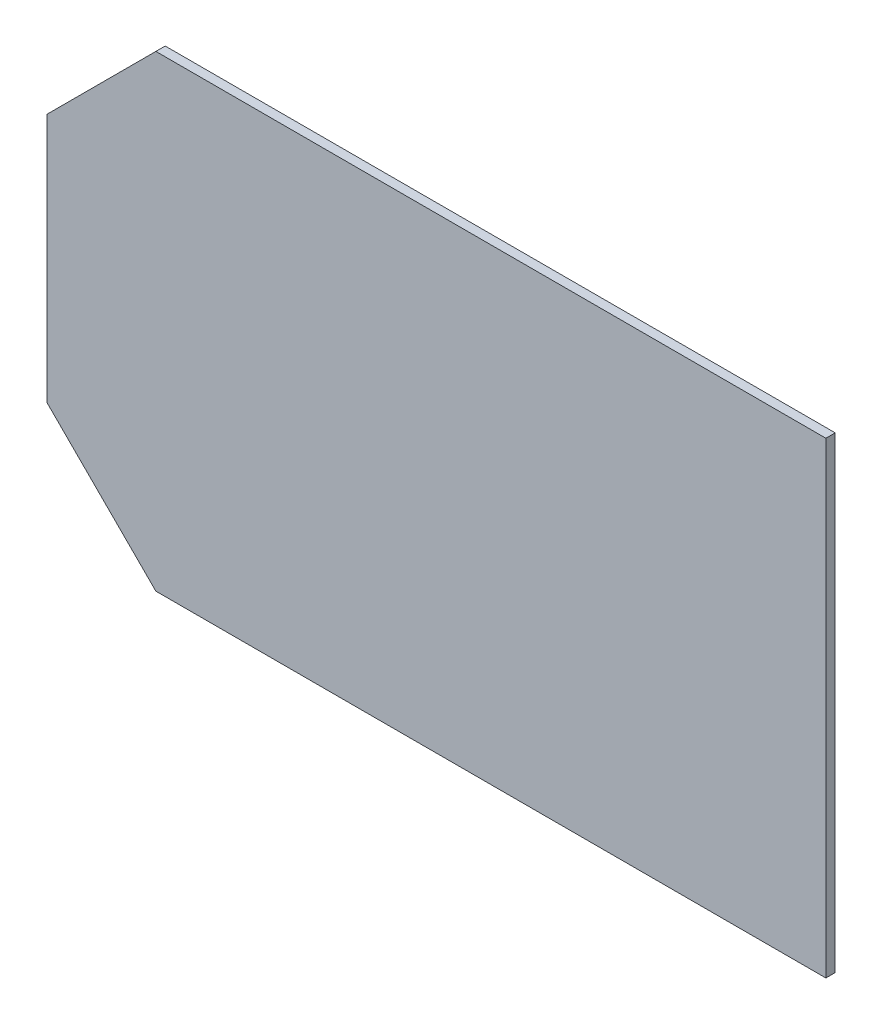
SolidWorks part; units mm, degrees
ref_plane "Front Plane" through (0, 0, 0) normal (0, 0, 1) x (1, 0, 0)
ref_plane "Top Plane" through (0, 0, 0) normal (0, 1, 0) x (1, 0, 0)
ref_plane "Right Plane" through (0, 0, 0) normal (1, 0, 0) x (0, 0, -1)
sketch "Sketch1" plane through (0, 0, 0) normal (0, 0, 1) x (1, 0, 0)
  line L1 (-125, 75) -> (125, 75)
  line L2 (-125, 75) -> (-125, -75)
  line L3 (-125, -75) -> (125, -75)
  line L4 (125, 75) -> (125, -75)
  line L5 (-125, 75) -> (125, -75) construction
  line L6 (-125, -75) -> (125, 75) construction
  point P0 (0, 0)
  dimension "D1" = 150
  dimension "D2" = 250
extrude "Boss-Extrude1" add sketch "Sketch1" along normal blind 3
chamfer "Chamfer2" [suppressed] distance 35 angle 45
chamfer "Chamfer3" distance 35 angle 45 2 edges at (-125, -75, 1.5) (-125, 75, 1.5)
